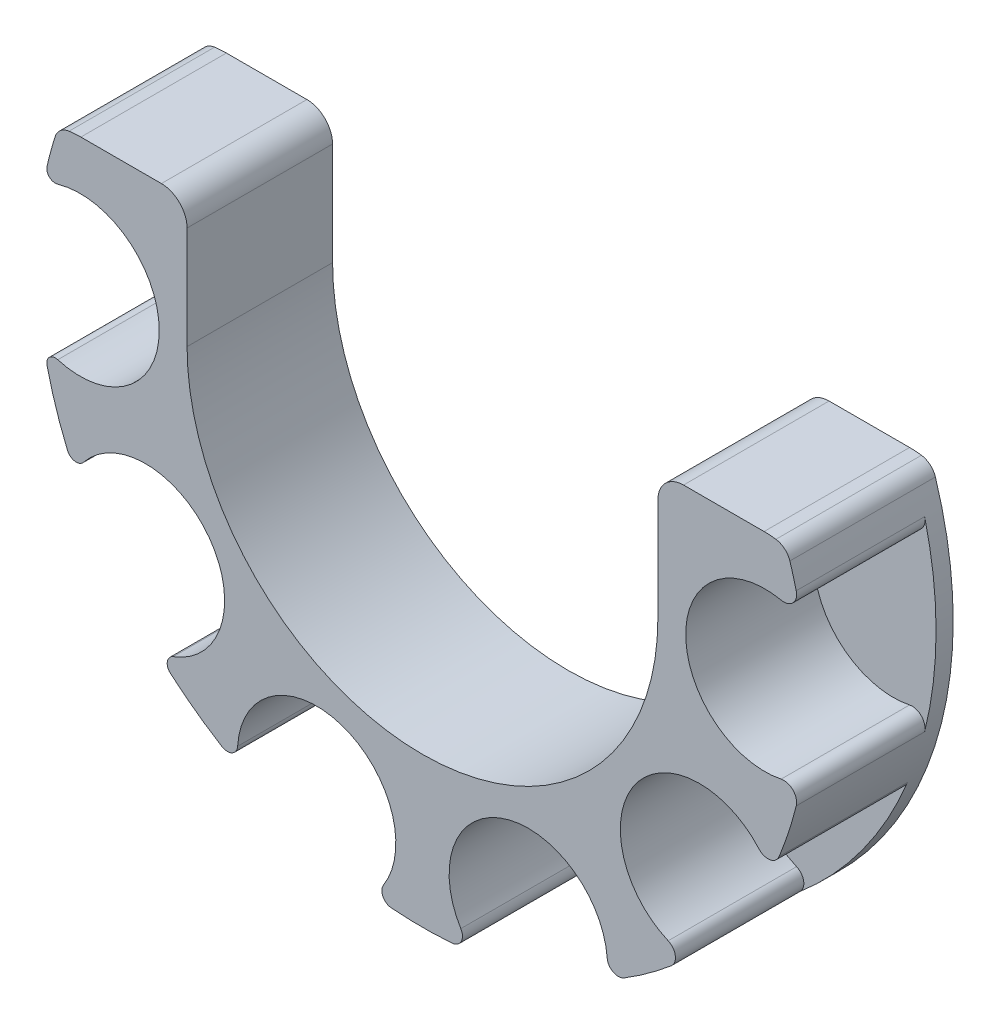
SolidWorks part; units mm, degrees
ref_plane "前视基准面" through (0, 0, 0) normal (0, 0, 1) x (1, 0, 0)
ref_plane "上视基准面" through (0, 0, 0) normal (0, 1, 0) x (1, 0, 0)
ref_plane "右视基准面" through (0, 0, 0) normal (1, 0, 0) x (0, 0, -1)
ref_plane "基准面4" through (0, 0, 0) normal (0, 0, -1) x (-1, 0, 0)
sketch "草图1" plane through (0, 0, 0) normal (0, 0, -1) x (-1, 0, 0)
  line L0 (-10.093, -187.6) -> (-89.907, -187.6)
  arc A0 (-7.4495, -187.9557) -> (-10.093, -187.6) centre (-10.093, -197.6) ccw
  arc A1 (-89.907, -187.6) -> (-92.5505, -187.9557) centre (-89.907, -197.6) ccw
  arc A2 (-92.5505, -187.9557) -> (-7.4495, -187.9557) centre (-50, -202.6) ccw
extrude "凸台-拉伸1" add sketch "草图1" against normal blind 17
sketch "草图2" plane through (0, 0, 17) normal (0, 0, 1) x (1, 0, 0)
  arc A0 (6.1386, -212.6586) -> (7.3949, -211.4756) centre (7.1133, -212.4351) cw
  arc A1 (7.3949, -211.4756) -> (7.3949, -193.7244) centre (10, -202.6) ccw
  arc A2 (7.3949, -193.7244) -> (6.1386, -192.5414) centre (7.1133, -192.7649) cw
  arc A3 (6.1386, -192.5414) -> (6.1386, -212.6586) centre (50, -202.6) ccw
extrude "切除-拉伸1" cut sketch "草图2" against normal blind 15
sketch "草图3" plane through (0, 0, 17) normal (0, 0, 1) x (1, 0, 0)
  arc A0 (20.5587, -236.6325) -> (20.8916, -234.7708) centre (21.2784, -235.8006) cw
  arc A1 (20.8916, -234.7708) -> (10.4088, -220.3424) centre (17.6393, -226.1114) ccw
  arc A2 (10.4088, -220.3424) -> (8.5353, -220.0837) centre (9.5489, -219.6564) cw
  arc A3 (8.5353, -220.0837) -> (20.5587, -236.6325) centre (50, -202.6) ccw
extrude "切除-拉伸2" cut sketch "草图3" against normal blind 15
sketch "草图4" plane through (0, 0, 17) normal (0, 0, 1) x (1, 0, 0)
  arc A0 (46.3561, -247.4522) -> (45.4412, -245.6115) centre (46.4533, -246.2562) cw
  arc A1 (45.4412, -245.6115) -> (28.4066, -240.0766) centre (37.6393, -240.6423) ccw
  arc A2 (28.4066, -240.0766) -> (26.5845, -241.028) centre (27.2089, -240.0033) cw
  arc A3 (26.5845, -241.028) -> (46.3561, -247.4522) centre (50, -202.6) ccw
extrude "切除-拉伸3" cut sketch "草图4" against normal blind 15
sketch "草图5" plane through (0, 0, 17) normal (0, 0, 1) x (1, 0, 0)
  arc A0 (73.5601, -240.9395) -> (71.5834, -239.9318) centre (72.8795, -239.8319) cw
  arc A1 (71.5834, -239.9318) -> (54.4818, -245.4884) centre (62.3607, -240.6423) ccw
  arc A2 (54.4818, -245.4884) -> (53.4749, -247.4656) centre (53.3745, -246.1695) cw
  arc A3 (53.4749, -247.4656) -> (73.5601, -240.9395) centre (50, -202.6) ccw
extrude "切除-拉伸4" cut sketch "草图5" against normal blind 15
sketch "草图6" plane through (0, 0, 17) normal (0, 0, 1) x (1, 0, 0)
  arc A0 (91.6597, -219.6139) -> (89.3116, -220.0083) centre (90.3636, -219.0846) cw
  arc A1 (89.3116, -220.0083) -> (78.7042, -234.608) centre (82.3607, -226.1114) ccw
  arc A2 (78.7042, -234.608) -> (79.0547, -236.9631) centre (78.1508, -235.894) cw
  arc A3 (79.0547, -236.9631) -> (91.6597, -219.6139) centre (50, -202.6) ccw
extrude "切除-拉伸5" cut sketch "草图6" against normal blind 15
sketch "草图7" plane through (0, 0, 17) normal (0, 0, 1) x (1, 0, 0)
  arc A0 (93.6641, -191.7165) -> (91.9004, -193.5473) centre (92.2086, -192.0793) cw
  arc A1 (91.9004, -193.5473) -> (91.9004, -211.6527) centre (90, -202.6) ccw
  arc A2 (91.9004, -211.6527) -> (93.6641, -213.4835) centre (92.2086, -213.1207) cw
  arc A3 (93.6641, -213.4835) -> (93.6641, -191.7165) centre (50, -202.6) ccw
extrude "切除-拉伸6" cut sketch "草图7" against normal blind 15
sketch "草图8" plane through (0, 0, 17) normal (0, 0, 1) x (1, 0, 0)
  line L0 (77.5, -187.6) -> (22.5, -187.6)
  line L1 (22.5, -187.6) -> (22.5, -202.6)
  line L2 (77.5, -202.6) -> (77.5, -187.6)
  arc A0 (22.5, -202.6) -> (77.5, -202.6) centre (50, -202.6) ccw
extrude "切除-拉伸7" cut sketch "草图8" against normal through all
fillet "圆角1" radius 2 2 edges at (7.4495, -187.9557, 8.5) (92.5505, -187.9557, 8.5)
fillet "圆角2" radius 3 2 edges at (22.5, -187.6, 8.5) (77.5, -187.6, 8.5)
